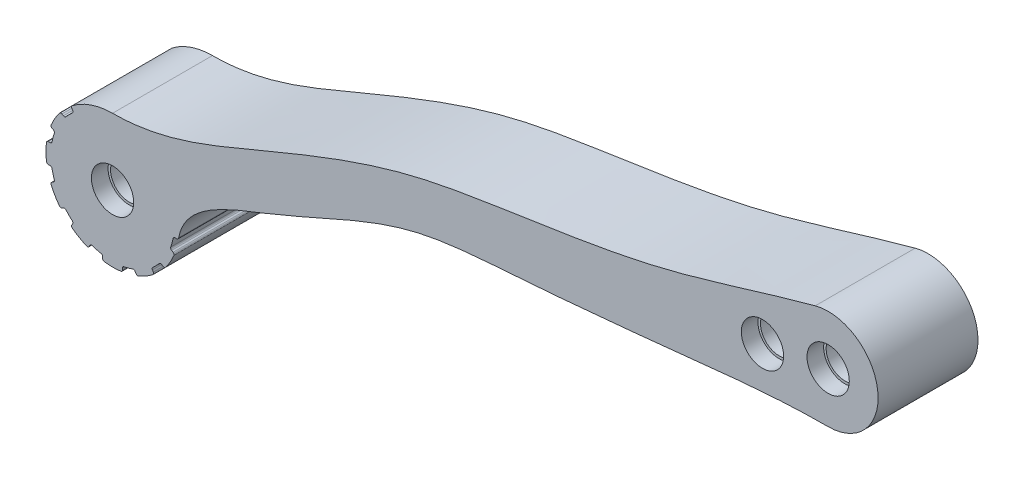
SolidWorks part; units mm, degrees
ref_plane "Alzado" through (0, 0, 0) normal (0, 0, 1) x (1, 0, 0)
ref_plane "Planta" through (0, 0, 0) normal (0, 1, 0) x (1, 0, 0)
ref_plane "Vista lateral" through (0, 0, 0) normal (1, 0, 0) x (0, 0, -1)
sketch "Croquis2" plane through (0, 0, 0) normal (0, 0, 1) x (1, 0, 0)
  line L0 (85.7307, 90.8821) -> (55.8025, 87.4231) construction
  line L1 (55.8025, 87.4231) -> (-37.1797, 50.6223) construction
  line L2 (55.8025, 87.4231) -> (54.5534, 93.2917) construction
  line L5 (55.8025, 87.4231) -> (57.4681, 79.5984) construction
  line L6 (54.5534, 93.2917) -> (57.4681, 79.5984) construction
  line L7 (9.3114, 69.0227) -> (6.5513, 75.9964) construction
  line L8 (9.3114, 69.0227) -> (12.0715, 62.049) construction
  line L9 (-37.1797, 50.6223) -> (-18.5833, 57.9825) construction
  line L11 (176.164, 120.1485) -> (180.0329, 105.656) construction
  line L12 (160.3129, 102.3215) -> (180.0329, 105.656) construction
  line L13 (180.0329, 105.656) -> (180.0329, 90.656) construction
  line L14 (194.8767, 103.497) -> (85.7307, 90.8821) construction
  line L17 (85.7307, 90.8821) -> (86.6492, 82.9351) construction
  line L19 (133.5731, 87.251) -> (130.2386, 106.971) construction
  line L20 (85.7307, 90.8821) -> (84.8121, 98.8292) construction
  line L21 (194.823, 108.1569) -> (107.6301, 93.4132) construction
  line L22 (-37.1797, 50.6223) -> (-32.506, 38.8135) construction
  line L23 (-34.8429, 44.7179) -> (-15.0578, 41.7938) construction
  line L24 (-34.8429, 44.7179) -> (-34.8429, 64.7179) construction
  arc A2 (180.0329, 90.656) -> (176.164, 120.1485) centre (180.0329, 105.656) ccw
  circle A5 centre (160.3129, 102.3215) radius 6.35
  circle A9 centre (180.0329, 105.656) radius 6.35
  circle A13 centre (-34.8429, 44.7179) radius 6.35
  arc A14 (-34.8429, 64.7179) -> (-15.0578, 41.7938) centre (-34.8429, 44.7179) ccw
  spline S0 degree 3 poles (-15.0578, 41.7938) (-13.4229, 52.8557) (19.9319, 63.7267) (50.0674, 80.6719) (92.8603, 83.1479) (133.3882, 87.0917) (164.2759, 90.656) (180.0329, 90.656) knots 0 0 0 0 0.164668 0.401388 0.54424 0.773428 1 1 1 1
  spline S1 degree 3 poles (176.164, 120.1485) (160.6443, 116.0053) (131.1643, 105.6378) (89.9022, 99.6371) (47.5779, 93.1694) (9.2636, 77.1449) (-20.3345, 64.7179) (-34.8429, 64.7179) knots 0 0 0 0 0.21855 0.429652 0.570361 0.803751 1 1 1 1
  dimension "D2" = 8
  dimension "D15" = 12.7
  dimension "D16" = 60
  dimension "D18" = 12.7
  dimension "D19" = 8
  dimension "D11" = 12.7
  dimension "D4" = 195
  dimension "D7" = 100
  dimension "D9" = 15
  dimension "D6" = 40
  dimension "D3" = 140
  dimension "D5" = 20
  dimension "D8" = 8
  dimension "D10" = 6
  dimension "D12" = 7.5
  dimension "D13" = 7.5
  dimension "D14" = 20
extrude "Saliente-Extruir1" add sketch "Croquis2" along normal blind 30
ref_plane "Plano1" through (0, 0, 30) normal (0, 0, 1) x (1, 0, 0)
sketch "Croquis5" plane through (0, 0, 0) normal (0, 0, -1) x (-1, 0, 0)
  circle A0 centre (-180.0329, 105.656) radius 2.5
  circle A1 centre (-180.0329, 105.656) radius 7.4433
  circle A2 centre (-160.3129, 102.3215) radius 2.5
  circle A3 centre (-160.3129, 102.3215) radius 7.335
extrude "Saliente-Extruir4" add sketch "Croquis5" against normal blind 30
sketch "Croquis6" plane through (0, 0, 0) normal (0, 0, -1) x (-1, 0, 0)
  circle A0 centre (-160.3129, 102.3215) radius 6.35
  circle A1 centre (-160.3129, 102.3215) radius 2.5
extrude "Cortar-Extruir2" cut sketch "Croquis6" against normal blind 5 contours A0
sketch "Croquis7" plane through (0, 0, 5) normal (0, 0, -1) x (-1, 0, 0)
  circle A0 centre (-160.3129, 102.3215) radius 5.6
  dimension "D1" = 11.2
extrude "Cortar-Extruir3" cut sketch "Croquis7" against normal blind 30 contours A0
sketch "Croquis8" plane through (0, 0, 30) normal (0, 0, 1) x (1, 0, 0)
  circle A0 centre (160.3129, 102.3215) radius 6.35
  circle A1 centre (160.3129, 102.3215) radius 5.6
  dimension "D1" = 12.7
  dimension "D2" = 11.2
extrude "Cortar-Extruir4" cut sketch "Croquis8" against normal blind 5
sketch "Croquis9" plane through (0, 0, 0) normal (0, 0, -1) x (-1, 0, 0)
  circle A1 centre (-180.0329, 105.656) radius 5.6
  circle A3 centre (-160.3129, 102.3215) radius 5.6 construction
extrude "Cortar-Extruir6" cut sketch "Croquis9" against normal blind 30
sketch "Croquis10" plane through (0, 0, 0) normal (0, 0, -1) x (-1, 0, 0)
  circle A0 centre (-180.0329, 105.656) radius 6.35
  circle A1 centre (-160.3129, 102.3215) radius 6.35 construction
extrude "Cortar-Extruir7" cut sketch "Croquis10" against normal blind 5
sketch "Croquis11" plane through (0, 0, 30) normal (0, 0, 1) x (1, 0, 0)
  circle A0 centre (180.0329, 105.656) radius 6.35
  circle A2 centre (160.3129, 102.3215) radius 6.35 construction
extrude "Cortar-Extruir8" cut sketch "Croquis11" against normal blind 5
sketch "Croquis14" plane through (0, 0, 0) normal (0, 0, -1) x (-1, 0, 0)
  circle A0 centre (34.8429, 44.7179) radius 6.35
  circle A1 centre (34.8429, 44.7179) radius 5.6
  dimension "D1" = 11.2
extrude "Saliente-Extruir5" add sketch "Croquis14" against normal blind 30
sketch "Croquis15" plane through (0, 0, 0) normal (0, 0, -1) x (-1, 0, 0)
  circle A1 centre (34.8429, 44.7179) radius 6.35
  dimension "D1" = 12.7
extrude "Cortar-Extruir9" cut sketch "Croquis15" against normal blind 5
sketch "Croquis16" plane through (0, 0, 30) normal (0, 0, 1) x (1, 0, 0)
  circle A0 centre (-34.8429, 44.7179) radius 6.35
  dimension "D1" = 12.7
extrude "Cortar-Extruir10" cut sketch "Croquis16" against normal blind 5 contours A0
sketch "Croquis17" plane through (0, 0, 0) normal (0, 0, -1) x (-1, 0, 0)
  line L1 (37.8404, 25.4438) -> (37.8429, 25.9619)
  line L2 (31.8453, 25.4438) -> (31.8429, 25.9619)
  line L3 (27.8017, 26.5273) -> (28.0629, 26.9747)
  line L4 (22.6099, 29.5248) -> (22.8668, 29.9747)
  line L5 (19.6498, 32.4849) -> (20.0997, 32.7418)
  line L6 (16.6522, 37.6768) -> (17.0997, 37.938)
  line L7 (15.5688, 41.7204) -> (16.0869, 41.7179)
  line L8 (15.5688, 47.7154) -> (16.0869, 47.7179)
  line L9 (16.6522, 51.759) -> (17.0997, 51.4978)
  line L10 (19.6498, 56.9509) -> (20.0997, 56.694)
  line L11 (22.6099, 59.911) -> (22.8668, 59.4611)
  line L12 (27.8017, 62.9085) -> (28.0629, 62.4611)
  line L13 (31.8453, 63.992) -> (31.8429, 63.4739)
  line L14 (37.8404, 63.992) -> (37.8429, 63.4739)
  line L15 (41.884, 62.9085) -> (41.6228, 62.4611)
  line L16 (47.0758, 59.911) -> (46.8189, 59.4611)
  line L17 (50.036, 56.9509) -> (49.586, 56.694)
  line L18 (53.0335, 51.759) -> (52.586, 51.4978)
  line L19 (54.117, 47.7154) -> (53.5989, 47.7179)
  line L20 (54.117, 41.7204) -> (53.5989, 41.7179)
  line L21 (53.0335, 37.6768) -> (52.586, 37.938)
  line L22 (50.036, 32.4849) -> (49.586, 32.7418)
  line L23 (47.0758, 29.5248) -> (46.8189, 29.9747)
  line L24 (41.884, 26.5273) -> (41.6228, 26.9747)
  line L26 (14.9991, 42.2229) -> (14.8108, 42.1993)
  arc A0 (17.3656, 50.7839) -> (16.6741, 48.2032) centre (34.8429, 44.7179) ccw
  arc A1 (32.3479, 24.8741) -> (37.3378, 24.8741) centre (34.8429, 44.7179) ccw
  arc A2 (37.3378, 24.8741) -> (37.8404, 25.4438) centre (37.2662, 25.4438) ccw
  arc A3 (38.3282, 26.5492) -> (37.8429, 25.9619) centre (38.4408, 25.9619) ccw
  arc A4 (31.3575, 26.5492) -> (31.8429, 25.9619) centre (31.2449, 25.9619) cw
  arc A5 (32.3479, 24.8741) -> (31.8453, 25.4438) centre (32.4195, 25.4438) cw
  arc A6 (22.7603, 28.7802) -> (27.0817, 26.2852) centre (34.8429, 44.7179) ccw
  arc A7 (27.0817, 26.2852) -> (27.8017, 26.5273) centre (27.3045, 26.8144) ccw
  arc A8 (28.7769, 27.2407) -> (28.0629, 26.9747) centre (28.5808, 26.6757) ccw
  arc A9 (22.7603, 28.7802) -> (22.6099, 29.5248) centre (23.1071, 29.2377) cw
  arc A10 (22.7401, 30.726) -> (22.8668, 29.9747) centre (22.3489, 30.2737) cw
  arc A11 (16.4102, 36.9568) -> (18.9051, 32.6353) centre (34.8429, 44.7179) ccw
  arc A12 (18.9051, 32.6353) -> (19.6498, 32.4849) centre (19.3627, 32.9822) ccw
  arc A13 (20.8509, 32.6152) -> (20.0997, 32.7418) centre (20.3987, 32.224) ccw
  arc A14 (16.4102, 36.9568) -> (16.6522, 37.6768) centre (16.9393, 37.1796) cw
  arc A15 (17.3656, 38.6519) -> (17.0997, 37.938) centre (16.8007, 38.4559) cw
  arc A16 (14.9991, 47.2129) -> (14.9991, 42.2229) centre (34.8429, 44.7179) ccw
  arc A17 (14.9991, 42.2229) -> (15.5688, 41.7204) centre (15.5688, 42.2945) ccw
  arc A18 (16.6741, 41.2326) -> (16.0869, 41.7179) centre (16.0869, 41.1199) ccw
  arc A19 (14.9991, 47.2129) -> (15.5688, 47.7154) centre (15.5688, 47.1413) cw
  arc A20 (16.6741, 48.2032) -> (16.0869, 47.7179) centre (16.0869, 48.3159) cw
  arc A21 (18.9051, 56.8005) -> (16.4102, 52.4791) centre (34.8429, 44.7179) ccw
  arc A22 (16.4102, 52.4791) -> (16.6522, 51.759) centre (16.9393, 52.2563) ccw
  arc A23 (17.3656, 50.7839) -> (17.0997, 51.4978) centre (16.8007, 50.98) ccw
  arc A24 (18.9051, 56.8005) -> (19.6498, 56.9509) centre (19.3627, 56.4537) cw
  arc A25 (20.8509, 56.8207) -> (20.0997, 56.694) centre (20.3987, 57.2119) cw
  arc A26 (27.0817, 63.1506) -> (22.7603, 60.6556) centre (34.8429, 44.7179) ccw
  arc A27 (22.7603, 60.6556) -> (22.6099, 59.911) centre (23.1071, 60.1981) ccw
  arc A28 (22.7401, 58.7098) -> (22.8668, 59.4611) centre (22.3489, 59.1621) ccw
  arc A29 (27.0817, 63.1506) -> (27.8017, 62.9085) centre (27.3045, 62.6215) cw
  arc A30 (28.7769, 62.1952) -> (28.0629, 62.4611) centre (28.5808, 62.7601) cw
  arc A31 (37.3378, 64.5617) -> (32.3479, 64.5617) centre (34.8429, 44.7179) ccw
  arc A32 (32.3479, 64.5617) -> (31.8453, 63.992) centre (32.4195, 63.992) ccw
  arc A33 (31.3575, 62.8866) -> (31.8429, 63.4739) centre (31.2449, 63.4739) ccw
  arc A34 (37.3378, 64.5617) -> (37.8404, 63.992) centre (37.2662, 63.992) cw
  arc A35 (38.3282, 62.8866) -> (37.8429, 63.4739) centre (38.4408, 63.4739) cw
  arc A36 (46.9255, 60.6556) -> (42.604, 63.1506) centre (34.8429, 44.7179) ccw
  arc A37 (42.604, 63.1506) -> (41.884, 62.9085) centre (42.3812, 62.6215) ccw
  arc A38 (40.9088, 62.1952) -> (41.6228, 62.4611) centre (41.1049, 62.7601) ccw
  arc A39 (46.9255, 60.6556) -> (47.0758, 59.911) centre (46.5786, 60.1981) cw
  arc A40 (46.9456, 58.7098) -> (46.8189, 59.4611) centre (47.3368, 59.1621) cw
  arc A41 (53.2756, 52.4791) -> (50.7806, 56.8005) centre (34.8429, 44.7179) ccw
  arc A42 (50.7806, 56.8005) -> (50.036, 56.9509) centre (50.323, 56.4537) ccw
  arc A43 (48.8348, 56.8207) -> (49.586, 56.694) centre (49.287, 57.2119) ccw
  arc A44 (53.2756, 52.4791) -> (53.0335, 51.759) centre (52.7464, 52.2563) cw
  arc A45 (52.3201, 50.7839) -> (52.586, 51.4978) centre (52.885, 50.98) cw
  arc A46 (54.6866, 42.2229) -> (54.6866, 47.2129) centre (34.8429, 44.7179) ccw
  arc A47 (54.6866, 47.2129) -> (54.117, 47.7154) centre (54.117, 47.1413) ccw
  arc A48 (53.0116, 48.2032) -> (53.5989, 47.7179) centre (53.5989, 48.3159) ccw
  arc A49 (54.6866, 42.2229) -> (54.117, 41.7204) centre (54.117, 42.2945) cw
  arc A50 (53.0116, 41.2326) -> (53.5989, 41.7179) centre (53.5989, 41.1199) cw
  arc A51 (50.7806, 32.6353) -> (53.2756, 36.9568) centre (34.8429, 44.7179) ccw
  arc A52 (53.2756, 36.9568) -> (53.0335, 37.6768) centre (52.7464, 37.1796) ccw
  arc A53 (52.3201, 38.6519) -> (52.586, 37.938) centre (52.885, 38.4559) ccw
  arc A54 (50.7806, 32.6353) -> (50.036, 32.4849) centre (50.323, 32.9822) cw
  arc A55 (48.8348, 32.6152) -> (49.586, 32.7418) centre (49.287, 32.224) cw
  arc A56 (42.604, 26.2852) -> (46.9255, 28.7802) centre (34.8429, 44.7179) ccw
  arc A57 (46.9255, 28.7802) -> (47.0758, 29.5248) centre (46.5786, 29.2377) ccw
  arc A58 (46.9456, 30.726) -> (46.8189, 29.9747) centre (47.3368, 30.2737) ccw
  arc A59 (42.604, 26.2852) -> (41.884, 26.5273) centre (42.3812, 26.8144) cw
  arc A60 (40.9088, 27.2407) -> (41.6228, 26.9747) centre (41.1049, 26.6757) cw
  arc A61 (22.7401, 58.7098) -> (20.8509, 56.8207) centre (34.8429, 44.7179) ccw
  arc A62 (31.3575, 62.8866) -> (28.7769, 62.1952) centre (34.8429, 44.7179) ccw
  arc A63 (40.9088, 62.1952) -> (38.3282, 62.8866) centre (34.8429, 44.7179) ccw
  arc A64 (48.8348, 56.8207) -> (46.9456, 58.7098) centre (34.8429, 44.7179) ccw
  arc A65 (53.0116, 48.2032) -> (52.3201, 50.7839) centre (34.8429, 44.7179) ccw
  arc A66 (52.3201, 38.6519) -> (53.0116, 41.2326) centre (34.8429, 44.7179) ccw
  arc A67 (46.9456, 30.726) -> (48.8348, 32.6152) centre (34.8429, 44.7179) ccw
  arc A68 (38.3282, 26.5492) -> (40.9088, 27.2407) centre (34.8429, 44.7179) ccw
  arc A69 (28.7769, 27.2407) -> (31.3575, 26.5492) centre (34.8429, 44.7179) ccw
  arc A70 (20.8509, 32.6152) -> (22.7401, 30.726) centre (34.8429, 44.7179) ccw
  arc A71 (16.6741, 41.2326) -> (17.3656, 38.6519) centre (34.8429, 44.7179) ccw
  circle A72 centre (34.8429, 44.7179) radius 20
  spline S0 degree 1 poles (15.5688, 41.7204) (15.181, 41.7086) knots 0 0 1 1
  dimension "D1" = 12
extrude "Cortar-Extruir11" cut sketch "Croquis17" against normal blind 30
sketch "Croquis19" plane through (0, 0, 0) normal (0, 0, -1) x (-1, 0, 0)
  line L1 (14.6166, 43.2019) -> (14.8095, 41.6457)
  line L2 (14.8095, 41.6457) -> (15.218, 41.5713)
  line L3 (15.218, 41.5713) -> (15.5688, 41.7204)
  line L4 (15.5688, 41.7204) -> (15.218, 41.5713)
  arc A0 (14.9991, 42.2229) -> (15.5688, 41.7204) centre (15.595, 42.3243) ccw
  spline S0 degree 3 poles (14.9991, 42.2229) (14.8871, 42.5551) (14.7539, 42.8796) (14.6166, 43.2019) knots 0 0 0 0 1 1 1 1
extrude "Cortar-Extruir12" cut sketch "Croquis19" against normal blind 30 contours A0 S0 L1 L2 L3
sketch "Croquis20" plane through (0, 0, 0) normal (0, 0, -1) x (-1, 0, 0)
  line L0 (-160.3129, 102.3215) -> (-140.5928, 98.987)
  line L1 (-194.823, 108.1569) -> (-107.6301, 93.4132) construction
  line L2 (-140.5928, 98.987) -> (-139.2782, 106.7614)
  line L3 (-138.8614, 109.2265) -> (-142.4294, 88.1253)
  line L4 (-140.5928, 98.987) -> (-142.0126, 90.5904)
  line L5 (-57.4681, 79.5984) -> (-54.5534, 93.2917)
  line L6 (-54.5534, 93.2917) -> (-55.0738, 90.8464)
  line L7 (-55.0738, 90.8464) -> (-56.9476, 82.0437)
  line L8 (-84.8121, 98.8292) -> (-85.0992, 96.3458)
  line L9 (-85.7307, 90.8821) -> (-84.8121, 98.8292) construction
  circle A1 centre (34.8429, 44.7179) radius 20
  spline S0 degree 3 poles (4.769, 54.6159) (-10.5748, 61.0985) (-30.5896, 71.0963) (-61.215, 81.4887) (-85.3163, 82.6725) (-126.1116, 86.2104) (-157.1989, 90.0488) (-180.0329, 90.656) knots 0 0 0 0 0.262545 0.352939 0.507351 0.63981 1 1 1 1
  spline S1 degree 3 poles (15.0578, 41.7938) (13.4229, 52.8557) (-19.9319, 63.7267) (-50.0674, 80.6719) (-92.8603, 83.1479) (-133.3882, 87.0917) (-164.2759, 90.656) (-180.0329, 90.656) knots 0 0 0 0 0.164668 0.401388 0.54424 0.773428 1 1 1 1 construction
  spline S2 degree 3 poles (-176.164, 120.1485) (-164.5929, 117.0634) (-149.4621, 112.0673) (-125.9825, 105.7193) (-106.954, 102.1164) (-86.6047, 99.1081) (-69.5421, 96.5262) (-55.3957, 93.6972) (-37.1498, 88.4343) (-21.2919, 82.1713) (-3.0351, 74.5255) (13.1311, 67.7246) (27.3453, 64.7025) (34.8429, 64.7179) knots 0 0 0 0 0.164021 0.218226 0.333143 0.42905 0.500107 0.56958 0.626523 0.760063 0.802803 0.897808 1 1 1 1
  spline S3 degree 3 poles (-176.164, 120.1485) (-160.6443, 116.0053) (-131.1643, 105.6378) (-89.9022, 99.6371) (-47.5779, 93.1694) (-9.2636, 77.1449) (20.3345, 64.7179) (34.8429, 64.7179) knots 0 0 0 0 0.21855 0.429652 0.570361 0.803751 1 1 1 1 construction
  dimension "D1" = 40
  dimension "D2" = 20
  dimension "D3" = 2.5
  dimension "D4" = 2.5
  dimension "D5" = 2.5
  dimension "D6" = 2.5
  dimension "D7" = 2.5
